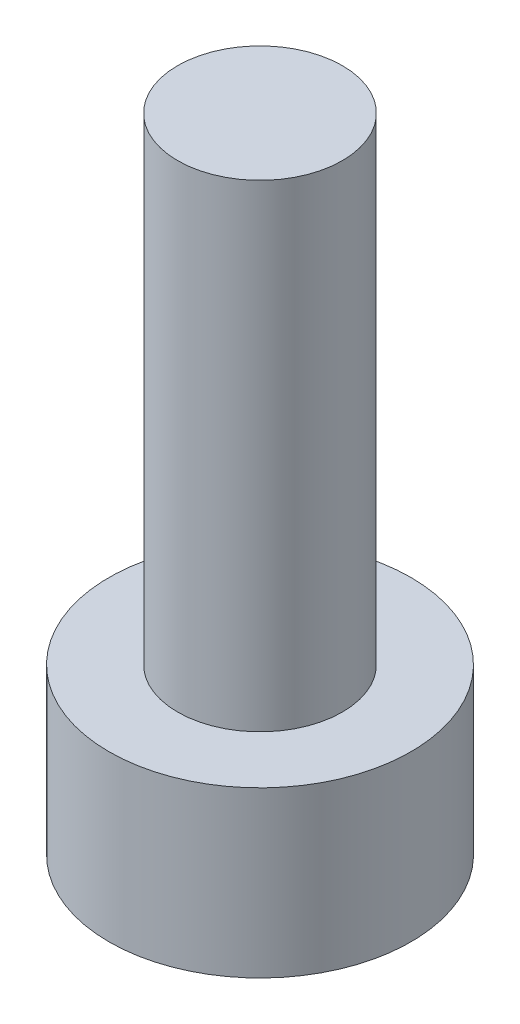
SolidWorks part; units mm, degrees
ref_plane "Front Plane" through (0, 0, 0) normal (0, 0, 1) x (1, 0, 0)
ref_plane "Top Plane" through (0, 0, 0) normal (0, 1, 0) x (1, 0, 0)
ref_plane "Right Plane" through (0, 0, 0) normal (1, 0, 0) x (0, 0, -1)
sketch "Sketch1" plane through (0, 0, 0) normal (0, 1, 0) x (1, 0, 0)
  circle A0 centre (0, 0) radius 2.75
  dimension "D1" = 5.5
extrude "Boss-Extrude1" add sketch "Sketch1" along normal blind 3
sketch "Sketch2" plane through (0, 3, 0) normal (0, 1, 0) x (1, 0, 0)
  circle A0 centre (0, 0) radius 1.5
  dimension "D1" = 3
extrude "Boss-Extrude2" add sketch "Sketch2" along normal blind 8.7
